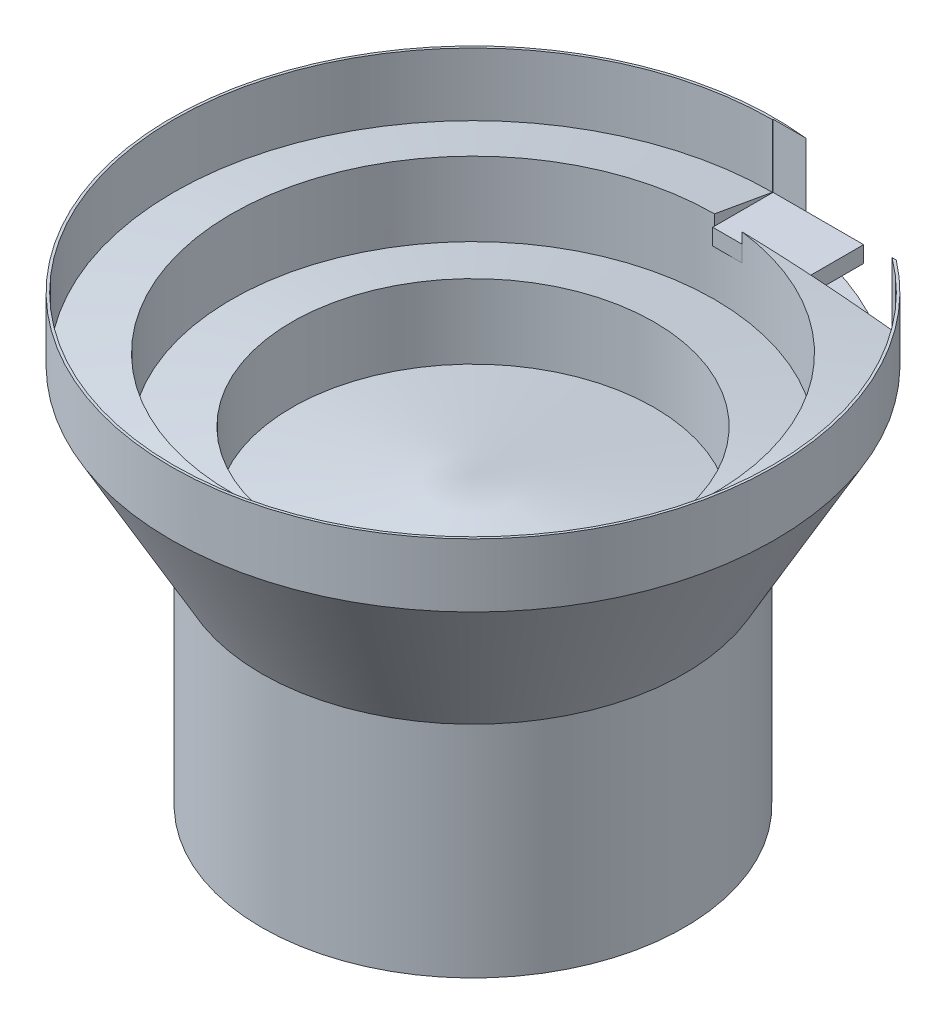
SolidWorks part; units mm, degrees
ref_plane "Front Plane" through (0, 0, 0) normal (0, 0, 1) x (1, 0, 0)
ref_plane "Top Plane" through (0, 0, 0) normal (0, 1, 0) x (1, 0, 0)
ref_plane "Right Plane" through (0, 0, 0) normal (1, 0, 0) x (0, 0, -1)
sketch "Sketch1" plane through (0, 0, 0) normal (0, 1, 0) x (1, 0, 0)
  circle A0 centre (0, 0) radius 350
  dimension "D1" = 700
extrude "Boss-Extrude1" add sketch "Sketch1" along normal blind 364
sketch "Sketch3" plane through (0, 0, 0) normal (1, 0, 0) x (0, 0, -1)
  line L0 (350, 364) -> (500, 631)
  line L1 (350, 364) -> (0, 364)
  line L2 (350, 364) -> (-350, 364) construction
  line L3 (0, 364) -> (0, 736) construction
  line L4 (500, 631) -> (500, 736)
  line L5 (495.8465, 631.7324) -> (400, 648.6327)
  line L6 (400, 648.6327) -> (400, 526)
  line L7 (400, 526) -> (300, 543.6327)
  line L8 (300, 543.6327) -> (300, 421)
  line L9 (300, 421) -> (0, 473.8981)
  line L10 (0, 473.8981) -> (0, 364)
  line L11 (500, 736) -> (495.8465, 736)
  line L12 (495.8465, 736) -> (495.8465, 631.7324)
  dimension "D1" = 372
  dimension "D2" = 100
  dimension "D3" = 100
  dimension "D4" = 80
  dimension "D5" = 80
  dimension "D6" = 500
  dimension "D7" = 105
  dimension "D8" = 105
  dimension "D9" = 105
  dimension "D10" = 80
  dimension "D11" = 109.8981
revolve "Revolve1" add sketch "Sketch3" angle 360 about L3
ref_plane "Plane1" through (0, 604, 0) normal (0, -1, 0) x (-1, 0, 0)
sketch "Sketch6" plane through (0, 604, 0) normal (0, -1, 0) x (-1, 0, 0)
  line L1 (0, 497) -> (-1000, 497)
  line L2 (0, 497) -> (0, 397)
  line L3 (0, 397) -> (-1000, 397)
  line L4 (-1000, 497) -> (-1000, 397)
  point P6 (0, 0)
  dimension "D1" = 1000
  dimension "D2" = 100
  dimension "D3" = 497
extrude "Cut-Extrude1" cut sketch "Sketch6" against normal through all
sketch "Sketch4" plane through (0, 604, 0) normal (0, 1, 0) x (1, 0, 0)
  line L0 (0, 497) -> (150, 497)
  line L1 (150, 497) -> (150, 397)
  line L2 (150, 397) -> (0, 397)
  line L3 (0, 397) -> (0, 497)
  dimension "D1" = 497
  dimension "D2" = 150
  dimension "D3" = 100
extrude "Boss-Extrude2" add sketch "Sketch4" along normal blind 27 separate body
